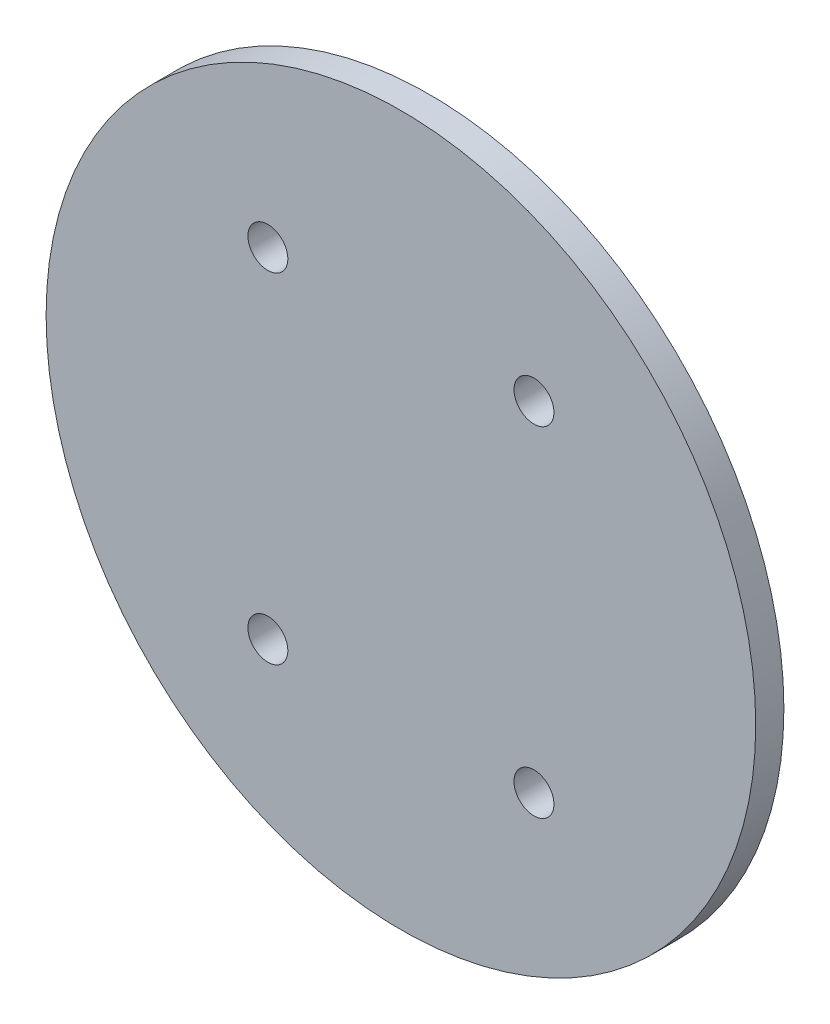
SolidWorks part; units mm, degrees
ref_plane "Front Plane" through (0, 0, 0) normal (0, 0, 1) x (1, 0, 0)
ref_plane "Top Plane" through (0, 0, 0) normal (0, 1, 0) x (1, 0, 0)
ref_plane "Right Plane" through (0, 0, 0) normal (1, 0, 0) x (0, 0, -1)
sketch "Sketch1" plane through (0, 0, 0) normal (0, 0, 1) x (1, 0, 0)
  circle A0 centre (0, 0) radius 40
  dimension "D1" = 80
extrude "Boss-Extrude1" add sketch "Sketch1" along normal mid plane 3.175
hole_wizard "M4 Clearance Hole1" positions "Sketch4" profile "Sketch3" hole size "M4" standard "ANSI Metric" end condition through all
sketch "Sketch4" plane through (0, 0, -1.5875) normal (0, 0, -1) x (-1, 0, 0)
  point P0 (15, 19.125)
  point P3 (-15, 19.125)
  point P6 (-15, -19.125)
  point P9 (15, -19.125)
sketch "Sketch3" plane through (-15, 19.125, -1.5875) normal (1, 0, 0) x (0, 1, 0)
  line L0 (0, 0) -> (0, 3.175)
  line L1 (0, 3.175) -> (2.25, 3.175)
  line L2 (2.25, 3.175) -> (2.25, 0)
  line L5 (2.25, 0) -> (0, 0)
  line L11 (0, -6.35) -> (0, 107.95) construction
  dimension "Thru Hole Dia." = 4.5
  dimension "Thru Hole Depth" = 3.175
